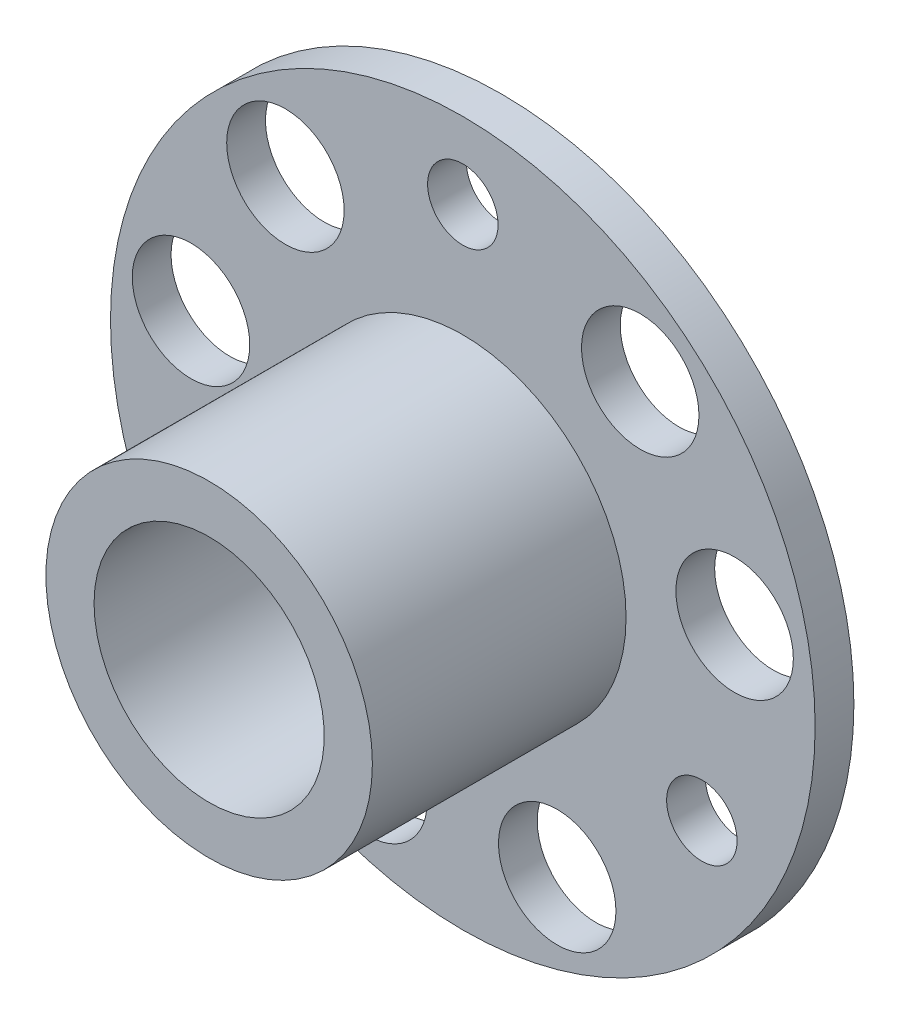
SolidWorks part; units mm, degrees
ref_plane "Front Plane" through (0, 0, 0) normal (0, 0, 1) x (1, 0, 0)
ref_plane "Top Plane" through (0, 0, 0) normal (0, 1, 0) x (1, 0, 0)
ref_plane "Right Plane" through (0, 0, 0) normal (1, 0, 0) x (0, 0, -1)
sketch "Sketch1" plane through (0, 0, 0) normal (0, 1, 0) x (1, 0, 0)
  line L0 (15, 0) -> (0, 0)
  line L1 (0, 0) -> (0, -1.65)
  line L2 (0, -1.65) -> (15, -1.65)
  line L3 (15, -1.65) -> (15, 0)
  line L4 (0, 0) -> (0, -1.65) construction
  dimension "D1" = 15
  dimension "D2" = 1.65
revolve "Revolve1" add sketch "Sketch1" angle 360 about L4
sketch "Sketch2" plane through (0, 0, 1.65) normal (0, 0, 1) x (1, 0, 0)
  circle A0 centre (0, 0) radius 6.95
  dimension "D1" = 13.9
extrude "Boss-Extrude1" add sketch "Sketch2" along normal blind 10.8
hole_wizard "Ø5.0 (5) Diameter Hole1" positions "Sketch4" profile "Sketch3" hole size "Ø5.0" standard "ANSI Metric"
sketch "Sketch4" plane through (0, 0, 0) normal (0, 0, -1) x (-1, 0, 0)
  point P0 (7.5528, 9.001)
  point P1 (11.5715, 2.0404)
  point P2 (4.0187, -11.0414)
  point P3 (-4.0187, -11.0414)
  point P4 (-11.5715, 2.0404)
  point P5 (-7.5528, 9.001)
sketch "Sketch3" plane through (-7.5528, 9.001, 0) normal (1, 0, 0) x (0, 1, 0)
  line L0 (0, 0) -> (0, 12.45)
  line L1 (0, 12.45) -> (2.5, 12.45)
  line L2 (2.5, 12.45) -> (2.5, 0)
  line L5 (2.5, 0) -> (0, 0)
  line L11 (0, -6.35) -> (0, 107.95) construction
  dimension "Thru Hole Dia." = 5
  dimension "Thru Hole Depth" = 12.45
hole_wizard "Ø3.0 (3) Diameter Hole1" positions "Sketch6" profile "Sketch5" hole size "Ø3.0" standard "ANSI Metric"
sketch "Sketch6" plane through (0, 0, 0) normal (0, 0, -1) x (-1, 0, 0)
  point P0 (0, 11.75)
  point P1 (10.1758, -5.875)
  point P2 (-10.1758, -5.875)
sketch "Sketch5" plane through (0, 11.75, 0) normal (1, 0, 0) x (0, 1, 0)
  line L0 (0, 0) -> (0, 12.45)
  line L1 (0, 12.45) -> (1.5, 12.45)
  line L2 (1.5, 12.45) -> (1.5, 0)
  line L5 (1.5, 0) -> (0, 0)
  line L11 (0, -6.35) -> (0, 107.95) construction
  dimension "Thru Hole Dia." = 3
  dimension "Thru Hole Depth" = 12.45
hole_wizard "Ø9.8 (9.8) Diameter Hole1" positions "Sketch8" profile "Sketch7" hole size "Ø9.8" standard "ANSI Metric"
sketch "Sketch8" plane through (0, 0, 0) normal (0, 0, -1) x (-1, 0, 0)
  point P0 (0, 0)
sketch "Sketch7" plane through (0, 0, 0) normal (1, 0, 0) x (0, 1, 0)
  line L0 (0, 0) -> (0, 12.45)
  line L1 (0, 12.45) -> (4.9, 12.45)
  line L2 (4.9, 12.45) -> (4.9, 0)
  line L5 (4.9, 0) -> (0, 0)
  line L11 (0, -6.35) -> (0, 107.95) construction
  dimension "Thru Hole Dia." = 9.8
  dimension "Thru Hole Depth" = 12.45
fillet "Fillet1" radius 0.5 1 edges at (-4.9, 0, 0)
